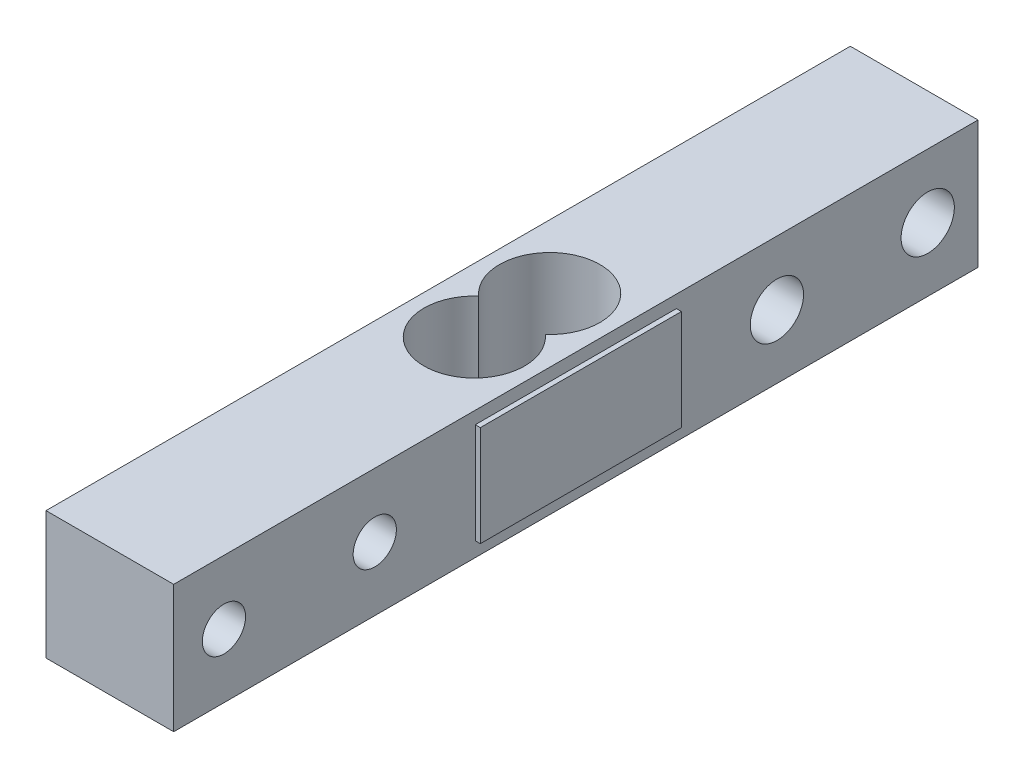
SolidWorks part; units mm, degrees
material "Plain Carbon Steel"
ref_plane "Front Plane" through (0, 0, 0) normal (0, 0, 1) x (1, 0, 0)
ref_plane "Top Plane" through (0, 0, 0) normal (0, 1, 0) x (1, 0, 0)
ref_plane "Right Plane" through (0, 0, 0) normal (1, 0, 0) x (0, 0, -1)
sketch "Sketch1" plane through (0, 0, 0) normal (1, 0, 0) x (0, 0, -1)
  line L1 (40, -6.35) -> (-40, -6.35)
  line L2 (40, -6.35) -> (40, 6.35)
  line L3 (40, 6.35) -> (-40, 6.35)
  line L4 (-40, -6.35) -> (-40, 6.35)
  line L5 (40, -6.35) -> (-40, 6.35) construction
  line L6 (40, 6.35) -> (-40, -6.35) construction
  point P0 (0, 0)
  dimension "D1" = 80
  dimension "D2" = 12.7
extrude "Boss-Extrude1" add sketch "Sketch1" along normal blind 12.7
sketch "Sketch2" plane through (0, 6.35, 0) normal (0, 1, 0) x (1, 0, 0)
  line L0 (12.7, 0) -> (0, 0) construction
  line L1 (12.7, 40) -> (12.7, -40) construction
  line L2 (6.35, 40) -> (6.35, -40) construction
  line L3 (12.7, 40) -> (0, 40) construction
  line L4 (12.7, -40) -> (0, -40) construction
  line L5 (3.0428, 0) -> (9.6572, 0) construction
  circle A0 centre (6.35, -3.75) radius 5
  circle A1 centre (6.35, 3.75) radius 5
  dimension "D1" = 10
  dimension "D2" = 10
  dimension "D3" = 7.5
extrude "Cut-Extrude1" cut sketch "Sketch2" against normal through all contours A0 A1 | A0 A1 | A1 A0
sketch "Sketch3" plane through (12.7, 0, 0) normal (1, 0, 0) x (0, 0, -1)
  line L0 (-40, 0) -> (40, 0) construction
  line L1 (-40, 6.35) -> (-40, -6.35) construction
  line L2 (40, -6.35) -> (40, 6.35) construction
  line L3 (-35, -6.35) -> (-35, 6.35) construction
  line L4 (-40, -6.35) -> (40, -6.35) construction
  line L5 (40, 6.35) -> (-40, 6.35) construction
  line L6 (-20, 6.35) -> (-20, -6.35) construction
  line L7 (20, -6.35) -> (20, 6.35) construction
  line L8 (35, 6.35) -> (35, -6.35) construction
  circle A0 centre (-35, 0) radius 2.15
  circle A1 centre (-20, 0) radius 2.15
  circle A2 centre (20, 0) radius 2.65
  circle A3 centre (35, 0) radius 2.65
  dimension "D5" = 4.3
  dimension "D6" = 5.3
  dimension "D1" = 5
  dimension "D2" = 15
  dimension "D3" = 5
  dimension "D4" = 15
extrude "Cut-Extrude2" cut sketch "Sketch3" against normal through all
sketch "Sketch4" plane through (0, 6.35, 0) normal (0, 1, 0) x (1, 0, 0)
  line L0 (-1000, 0) -> (49000, 0) construction
  line L1 (0, 40) -> (0, -40) construction
  line L2 (-0.5, -10) -> (0, -10)
  line L3 (-0.5, -10) -> (-0.5, 10)
  line L4 (-0.5, 10) -> (0, 10)
  line L5 (0, -10) -> (0, 10)
  line L6 (-0.5, -10) -> (0, 10) construction
  line L7 (-0.5, 10) -> (0, -10) construction
  line L8 (12.7, 40) -> (12.7, -40) construction
  line L9 (13.2, -10) -> (12.7, -10)
  line L10 (13.2, -10) -> (13.2, 10)
  line L11 (13.2, 10) -> (12.7, 10)
  line L12 (12.7, -10) -> (12.7, 10)
  line L13 (13.2, -10) -> (12.7, 10) construction
  line L14 (13.2, 10) -> (12.7, -10) construction
  point P1 (-0.25, 0)
  point P10 (12.95, 0)
  dimension "D1" = 0.5
  dimension "D2" = 20
extrude "Boss-Extrude2" add sketch "Sketch4" against normal blind 10 from offset 1.25
